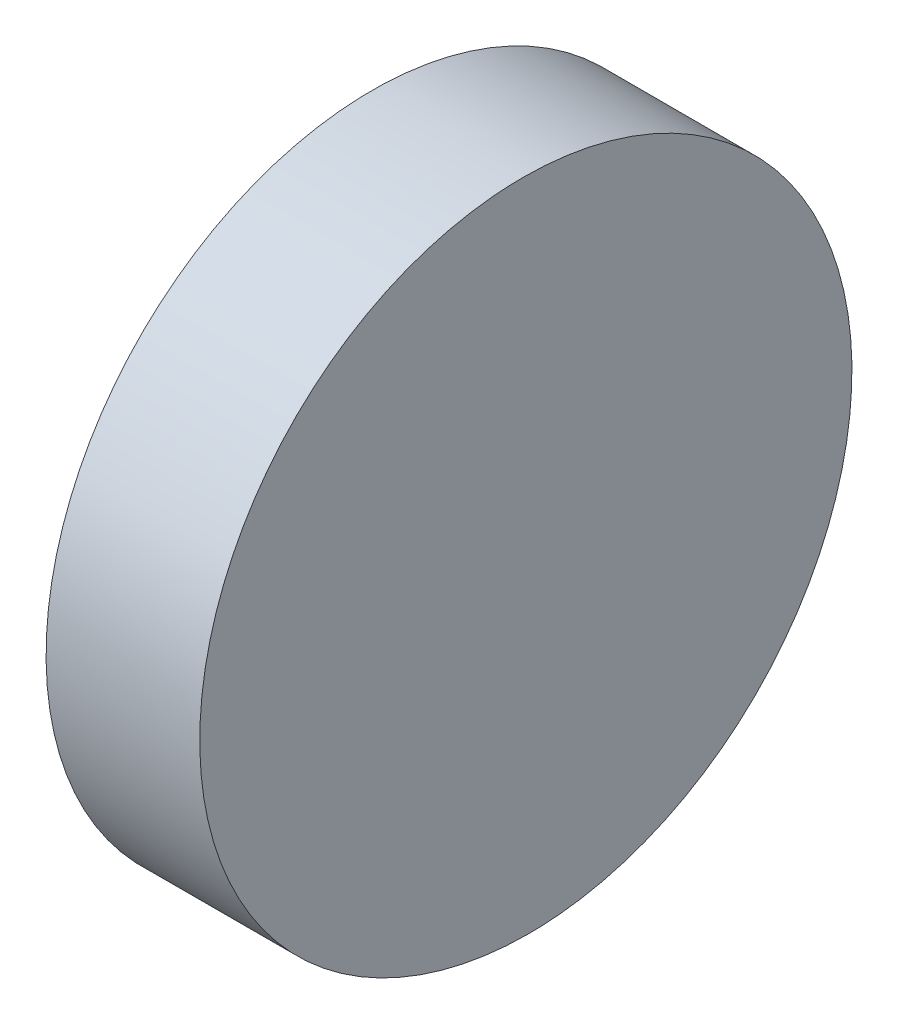
SolidWorks part; units mm, degrees
ref_plane "前视基准面" through (0, 0, 0) normal (0, 0, 1) x (1, 0, 0)
ref_plane "上视基准面" through (0, 0, 0) normal (0, 1, 0) x (1, 0, 0)
ref_plane "右视基准面" through (0, 0, 0) normal (1, 0, 0) x (0, 0, -1)
sketch "草图1" plane through (0, 0, 0) normal (0, 0, 1) x (1, 0, 0)
  line L0 (15.2768, 0) -> (-15.2768, 0) construction
  line L1 (0, 6.25) -> (0, -6.25)
  line L2 (0, -6.25) -> (3, -6.25)
  line L3 (3, -6.25) -> (2.8909, 6.25)
  line L4 (0, 6.25) -> (2.8909, 6.25)
  point P5 (0, 0)
  dimension "D1" = 3
  dimension "D2" = 12.5
  dimension "D3" = 0.5
extrude "凸台-拉伸1" add sketch "草图1" along normal blind 12.5 contours L1 L2 L3 L4
sketch "草图2" plane through (0, 0, 0) normal (-1, 0, 0) x (0, 0, 1)
  line L4 (0, 6.25) -> (0, -6.25)
  line L5 (0, -6.25) -> (12.5, -6.25)
  line L6 (12.5, -6.25) -> (12.5, 6.25)
  line L7 (12.5, 6.25) -> (0, 6.25)
  line L8 (0, 6.25) -> (0, -6.25)
  line L9 (0, -6.25) -> (12.5, -6.25)
  line L10 (12.5, -6.25) -> (12.5, 6.25)
  line L11 (12.5, 6.25) -> (0, 6.25)
  circle A0 centre (6.25, 0) radius 6.25
  line M1 (0, 6.25) -> (0, -6.25)
  line M2 (0, -6.25) -> (12.5, -6.25)
  line M3 (12.5, -6.25) -> (12.5, 6.25)
  line M4 (12.5, 6.25) -> (0, 6.25)
  dimension "D1" = 0
extrude "切除-拉伸1" cut sketch "草图2" against normal blind 10 contours A0 L8 M2 | A0 L9 M3 | A0 L10 M4 | A0 L11 M1
